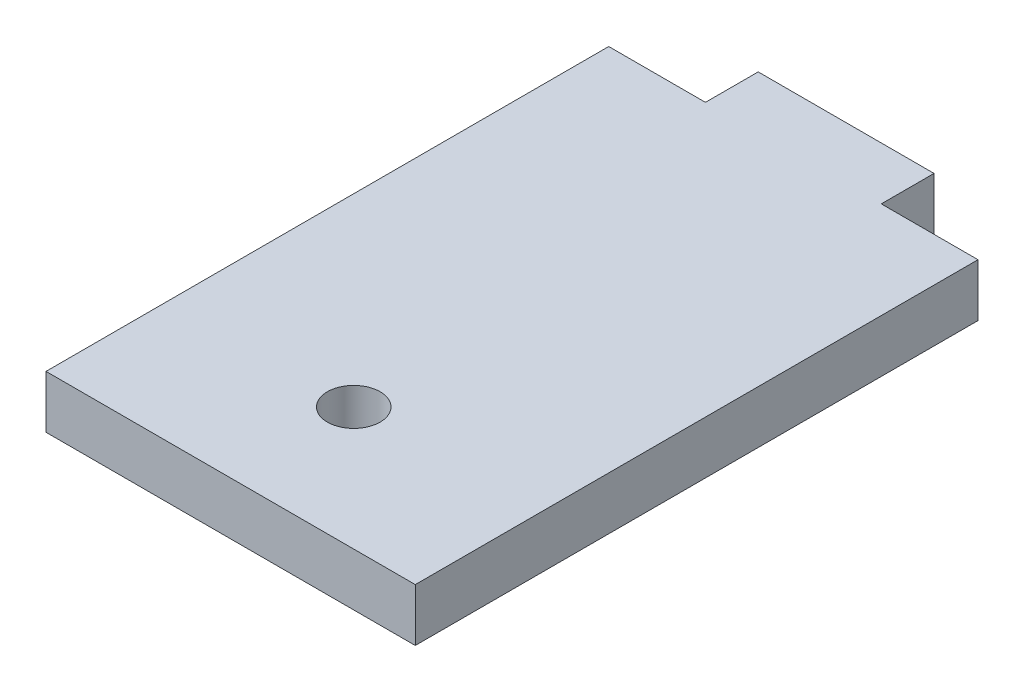
SolidWorks part; units mm, degrees
ref_plane "Alzado" through (0, 0, 0) normal (0, 0, 1) x (1, 0, 0)
ref_plane "Planta" through (0, 0, 0) normal (0, 1, 0) x (1, 0, 0)
ref_plane "Vista lateral" through (0, 0, 0) normal (1, 0, 0) x (0, 0, -1)
sketch "Croquis1" plane through (0, 0, 0) normal (0, 1, 0) x (1, 0, 0)
  line L0 (0, 0) -> (10, 0)
  line L1 (10, 0) -> (10, -3)
  line L2 (10, -3) -> (15.5, -3)
  line L3 (15.5, -3) -> (15.5, -35)
  line L4 (15.5, -35) -> (-5.5, -35)
  line L5 (-5.5, -35) -> (-5.5, -3)
  line L6 (-5.5, -3) -> (0, -3)
  line L7 (0, -3) -> (0, 0)
  line L8 (14, -3) -> (14, -35) construction
  circle A1 centre (5, -28) radius 1.5
  dimension "D7" = 7
  dimension "D8" = 3
  dimension "D1" = 10
  dimension "D2" = 3
  dimension "D3" = 35
  dimension "D4" = 21
  dimension "D5" = 5.5
  dimension "D6" = 19.5
  dimension "D9" = 10.5
extrude "Saliente-Extruir1" add sketch "Croquis1" along normal blind 3
